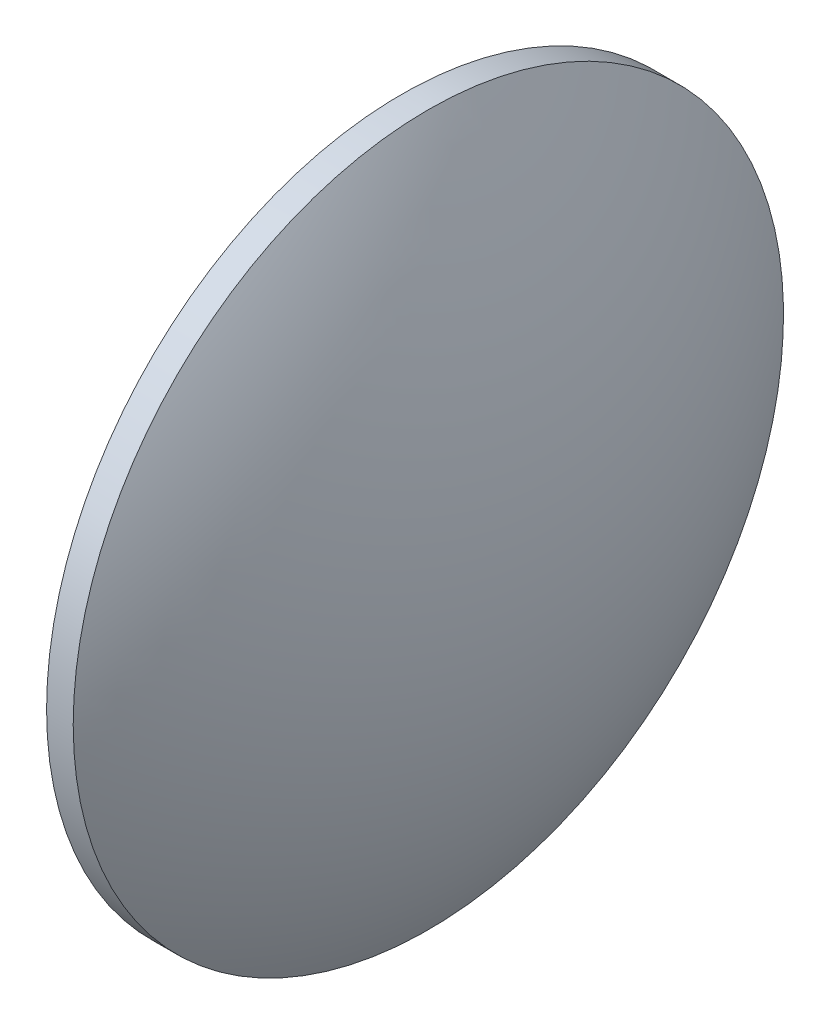
SolidWorks part; units mm, degrees
ref_plane "前视基准面" through (0, 0, 0) normal (0, 0, 1) x (1, 0, 0)
ref_plane "上视基准面" through (0, 0, 0) normal (0, 1, 0) x (1, 0, 0)
ref_plane "右视基准面" through (0, 0, 0) normal (1, 0, 0) x (0, 0, -1)
sketch "草图1" plane through (0, 0, 0) normal (0, 0, 1) x (1, 0, 0)
  line L0 (217.9946, 130.4671) -> (258.5717, 130.4671) construction
  line L1 (225.9491, 130.4671) -> (225.9491, 170.4671)
  line L2 (225.9491, 170.4671) -> (228.9491, 170.4671)
  line L3 (240.0691, 130.4671) -> (225.9491, 130.4671)
  arc A0 (240.0691, 130.4671) -> (228.9491, 170.4671) centre (162.5666, 130.4671) ccw
revolve "旋转1" add sketch "草图1" angle 360 about L0
